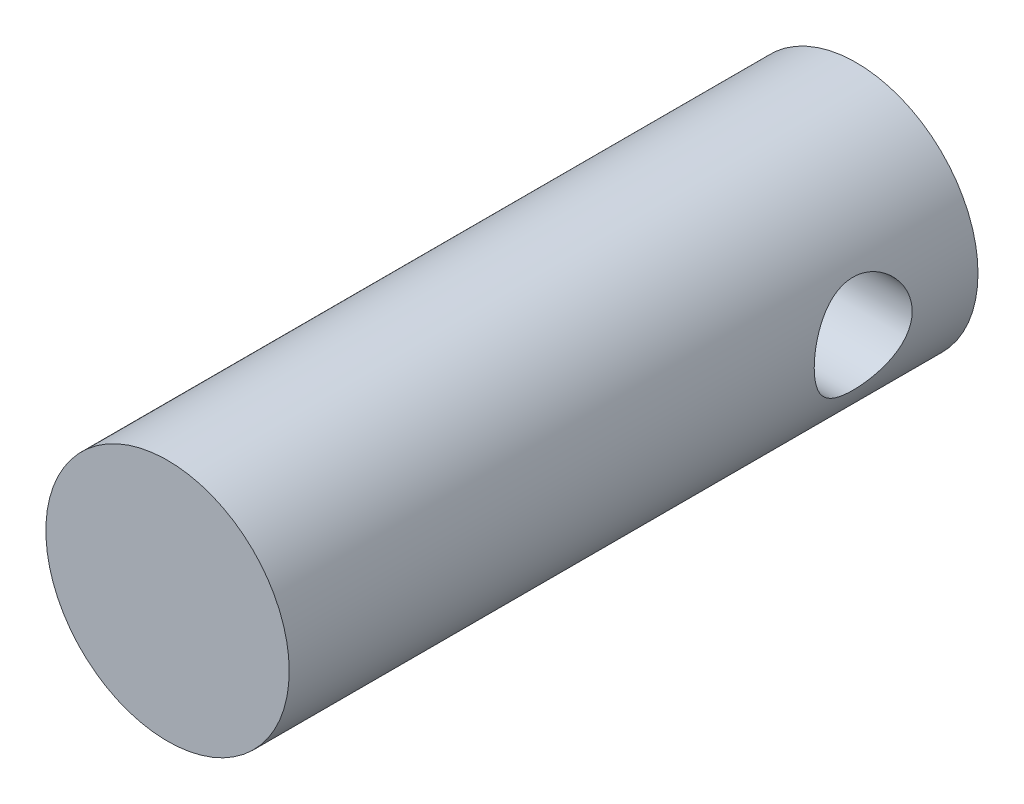
SolidWorks part; units mm, degrees
ref_plane "Front Plane" through (0, 0, 0) normal (0, 0, 1) x (1, 0, 0)
ref_plane "Top Plane" through (0, 0, 0) normal (0, 1, 0) x (1, 0, 0)
ref_plane "Right Plane" through (0, 0, 0) normal (1, 0, 0) x (0, 0, -1)
sketch "Sketch1" plane through (0, 0, 0) normal (0, 0, 1) x (1, 0, 0)
  circle A0 centre (0, 0) radius 15.9
extrude "Boss-Extrude1" add sketch "Sketch1" along normal blind 90
hole_wizard "Ø12.8 (12.8) Diameter Hole1" positions "3DSketch1" profile "Sketch2" hole size "Ø12.8" standard "Ansi Metric"
sketch3d "3DSketch1"
  line L0 (0, 0, 0) -> (15.9, 0, 0)
  line L1 (15.9, 0, 0) -> (15.9, 0, 15)
  circle A0 centre (0, 0, 0) radius 15.9 construction
  point P0 (15.9, 0, 15)
  point P7 (0, 0, 15.9)
  dimension "D1" = 15
sketch "Sketch2" plane through (15.9, 0, 15) normal (0, 1, 0) x (0, 0, -1)
  line L0 (0, 0) -> (0, 303.8455)
  line L1 (0, 303.8455) -> (6.4, 300)
  line L2 (6.4, 300) -> (6.4, 0)
  line L5 (6.4, 0) -> (0, 0)
  line L10 (0, 303.8455) -> (-6.4, 300) construction
  line L11 (0, -6.35) -> (0, 107.95) construction
  dimension "Hole Dia." = 12.8
  dimension "Hole Depth" = 300
  dimension "Drill Angle" = 118
